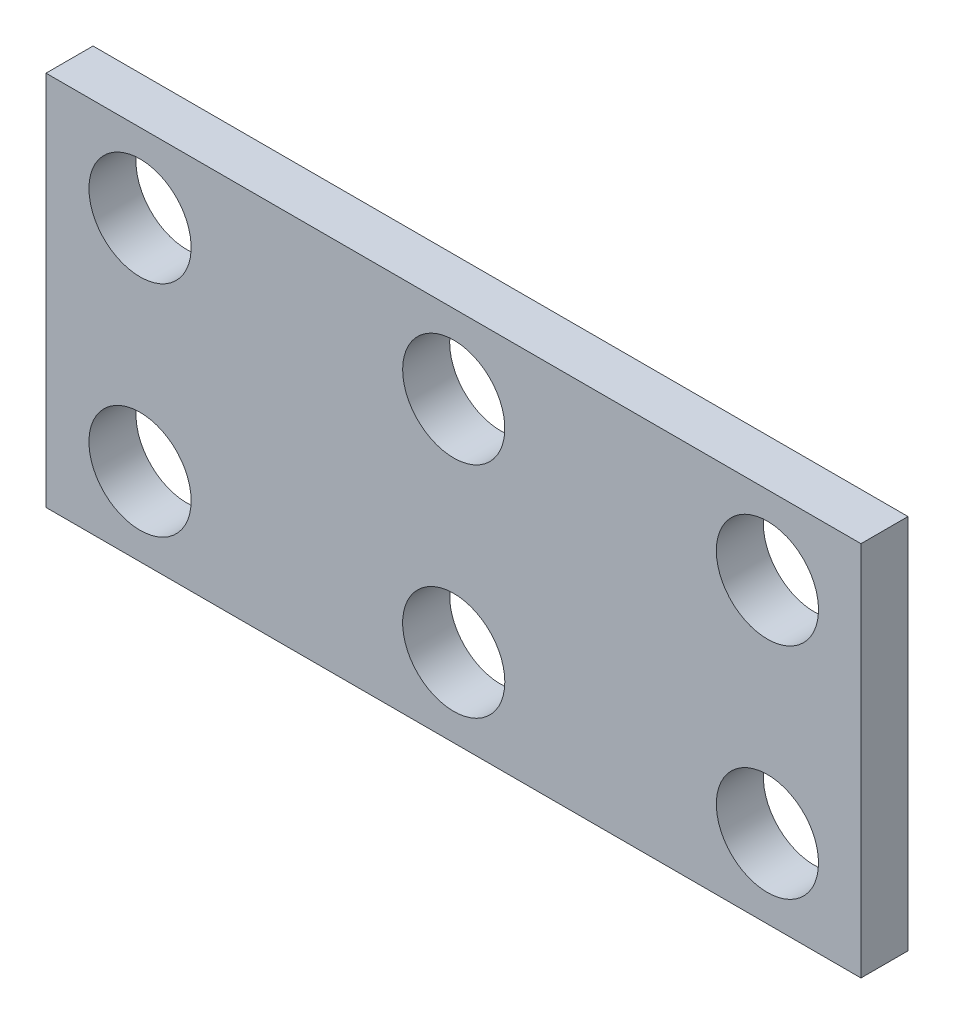
SolidWorks part; units mm, degrees
material "AISI 304"
ref_plane "Front" through (0, 0, 0) normal (0, 0, 1) x (1, 0, 0)
ref_plane "Top" through (0, 0, 0) normal (0, 1, 0) x (1, 0, 0)
ref_plane "Right" through (0, 0, 0) normal (1, 0, 0) x (0, 0, -1)
sketch "Sketch1" plane through (0, 0, 0) normal (0, 0, 1) x (1, 0, 0)
  line L1 (0, 0) -> (-26, 0)
  line L2 (0, 0) -> (0, 12)
  line L3 (0, 12) -> (-26, 12)
  line L4 (-26, 0) -> (-26, 12)
  dimension "D1" = 26
  dimension "D2" = 12
extrude "Extrude1" add sketch "Sketch1" against normal blind 1.5
sketch "Sketch2" plane through (0, 0, 0) normal (0, 0, 1) x (1, 0, 0)
  line L2 (-13, 12) -> (-13, 0) construction
  line L3 (0, 12) -> (-26, 12) construction
  line L4 (-26, 0) -> (0, 0) construction
  line L5 (-26, 6) -> (0, 6) construction
  line L6 (-26, 12) -> (-26, 0) construction
  line L7 (0, 0) -> (0, 12) construction
  circle A0 centre (-12.9924, 2.5) radius 1.63
  circle A1 centre (-2.9848, 2.5) radius 1.63
  circle A2 centre (-2.9848, 9.5) radius 1.63
  circle A3 centre (-12.9924, 9.5) radius 1.63
  circle A4 centre (-23, 2.5) radius 1.63
  circle A5 centre (-23, 9.5) radius 1.63
  dimension "D6" = 3.26
  dimension "D1" = 3
  dimension "D2" = 2.5
extrude "Extrude2" cut sketch "Sketch2" against normal through all
